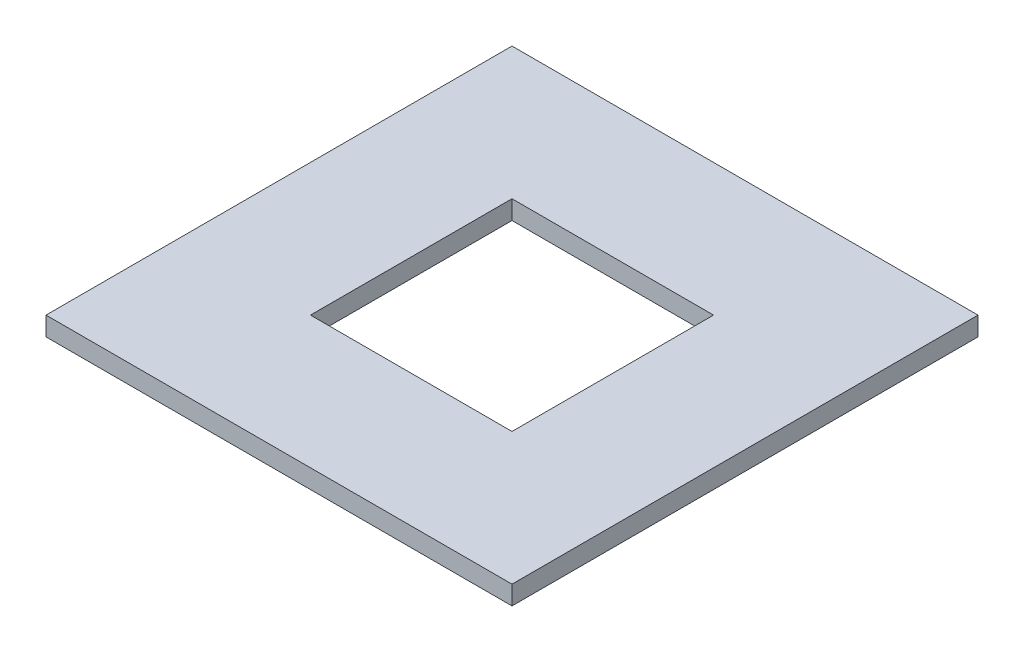
SolidWorks part; units mm, degrees
ref_plane "Front Plane" through (0, 0, 0) normal (0, 0, 1) x (1, 0, 0)
ref_plane "Top Plane" through (0, 0, 0) normal (0, 1, 0) x (1, 0, 0)
ref_plane "Right Plane" through (0, 0, 0) normal (1, 0, 0) x (0, 0, -1)
sketch "Sketch1" plane through (0, 0, 0) normal (0, 1, 0) x (1, 0, 0)
  line L1 (-37, 37) -> (37, 37)
  line L2 (-37, 37) -> (-37, -37)
  line L3 (-37, -37) -> (37, -37)
  line L4 (37, 37) -> (37, -37)
  line L5 (-16, -16) -> (16, -16)
  line L6 (-16, -16) -> (-16, 16)
  line L7 (-16, 16) -> (16, 16)
  line L8 (16, -16) -> (16, 16)
  point P4 (0, 37)
  point P6 (-37, 0)
  point P11 (16, 0)
  point P12 (0, 16)
  dimension "D1" = 74
  dimension "D2" = 32
  dimension "D3" = 32
extrude "Boss-Extrude1" add sketch "Sketch1" along normal blind 3
sketch "Sketch3" plane through (0, 0, 0) normal (0, 1, 0) x (1, 0, 0)
  line L0 (-22, 22) -> (-22, -22) construction
  line L1 (-22, -22) -> (22, -22) construction
  circle A0 centre (-22, 22) radius 1.8
  circle A1 centre (22, 22) radius 1.8
  circle A2 centre (22, -22) radius 1.8
  circle A3 centre (-22, -22) radius 1.8
  point P8 (0, -22)
  point P9 (-22, 0)
  dimension "D1" = 3.6
  dimension "D2" = 44
  dimension "D3" = 44
extrude "Cut-Extrude1" cut sketch "Sketch3" along normal blind 1.5
